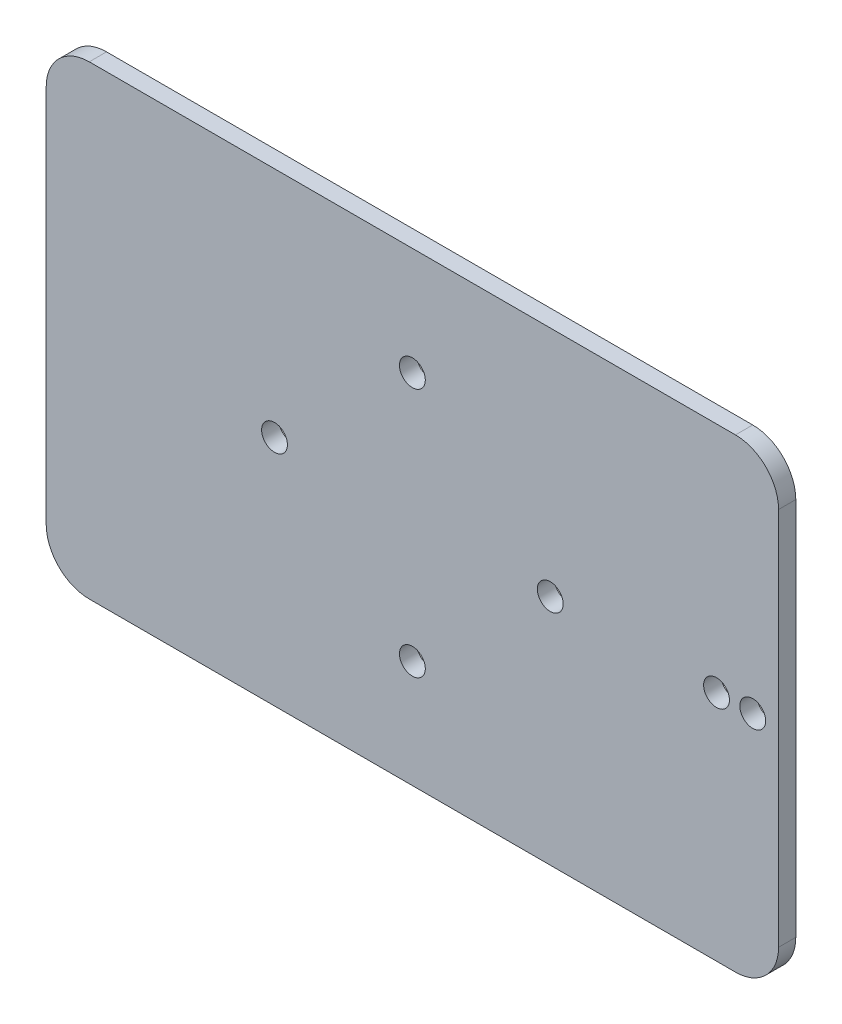
SolidWorks part; units mm, degrees
ref_plane "前视基准面" through (0, 0, 0) normal (0, 0, 1) x (1, 0, 0)
ref_plane "上视基准面" through (0, 0, 0) normal (0, 1, 0) x (1, 0, 0)
ref_plane "右视基准面" through (0, 0, 0) normal (1, 0, 0) x (0, 0, -1)
sketch "草图1" plane through (0, 0, 0) normal (0, 0, 1) x (1, 0, 0)
  line L0 (-42.5, 0) -> (0, 0) construction
  line L1 (-42.5, 27) -> (42.5, 27)
  line L2 (-42.5, 27) -> (-42.5, -27)
  line L3 (-42.5, -27) -> (42.5, -27)
  line L4 (42.5, 27) -> (42.5, -27)
  line L5 (-42.5, 27) -> (42.5, -27) construction
  line L6 (-42.5, -27) -> (42.5, 27) construction
  line L7 (0, 0) -> (42.5, 0) construction
  line L13 (0, 27) -> (0, 0) construction
  line L14 (0, 0) -> (0, -27) construction
  circle A0 centre (39.5, 0) radius 1.5
  circle A5 centre (35.3, 0) radius 1.5
  circle A6 centre (0, 14.5) radius 1.5
  circle A7 centre (-16, 0) radius 1.5
  circle A8 centre (16, 0) radius 1.5
  circle A9 centre (0, -14.5) radius 1.5
  point P0 (0, 0)
  dimension "D3" = 3
  dimension "D4" = 4.2
  dimension "D5" = 3
  dimension "D8" = 3
  dimension "D13" = 3
  dimension "D14" = 3
  dimension "D1" = 54
  dimension "D2" = 85
  dimension "D11" = 16
  dimension "D12" = 14.5
extrude "凸台-拉伸1" add sketch "草图1" along normal blind 2
fillet "圆角1" radius 5 4 edges at (-42.5, -27, 1) (42.5, -27, 1) (42.5, 27, 1) (-42.5, 27, 1)
